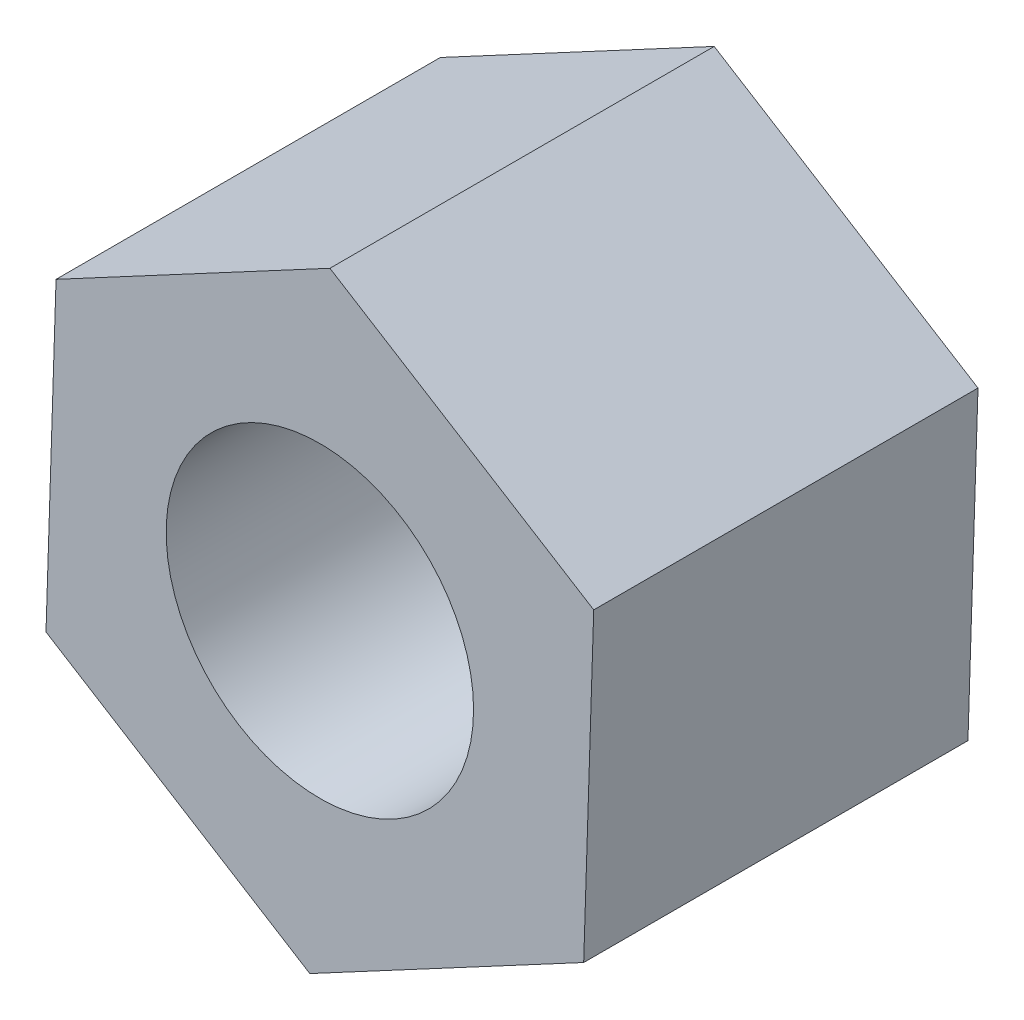
SolidWorks part; units mm, degrees
ref_plane "Front Plane" through (0, 0, 0) normal (0, 0, 1) x (1, 0, 0)
ref_plane "Top Plane" through (0, 0, 0) normal (0, 1, 0) x (1, 0, 0)
ref_plane "Right Plane" through (0, 0, 0) normal (1, 0, 0) x (0, 0, -1)
sketch "Sketch1" plane through (0, 0, 0) normal (0, 0, 1) x (1, 0, 0)
  line L1 (5.6572, 3.0263) -> (0.2077, 6.4124)
  line L2 (0.2077, 6.4124) -> (-5.4495, 3.3861)
  line L3 (-5.4495, 3.3861) -> (-5.6572, -3.0263)
  line L4 (-5.6572, -3.0263) -> (-0.2077, -6.4124)
  line L5 (-0.2077, -6.4124) -> (5.4495, -3.3861)
  line L6 (5.4495, -3.3861) -> (5.6572, 3.0263)
  circle A0 centre (0, 0) radius 5.5562 construction
  circle A1 centre (0, 0) radius 3.175
extrude "Extrude1" add sketch "Sketch1" along normal blind 7.9375
